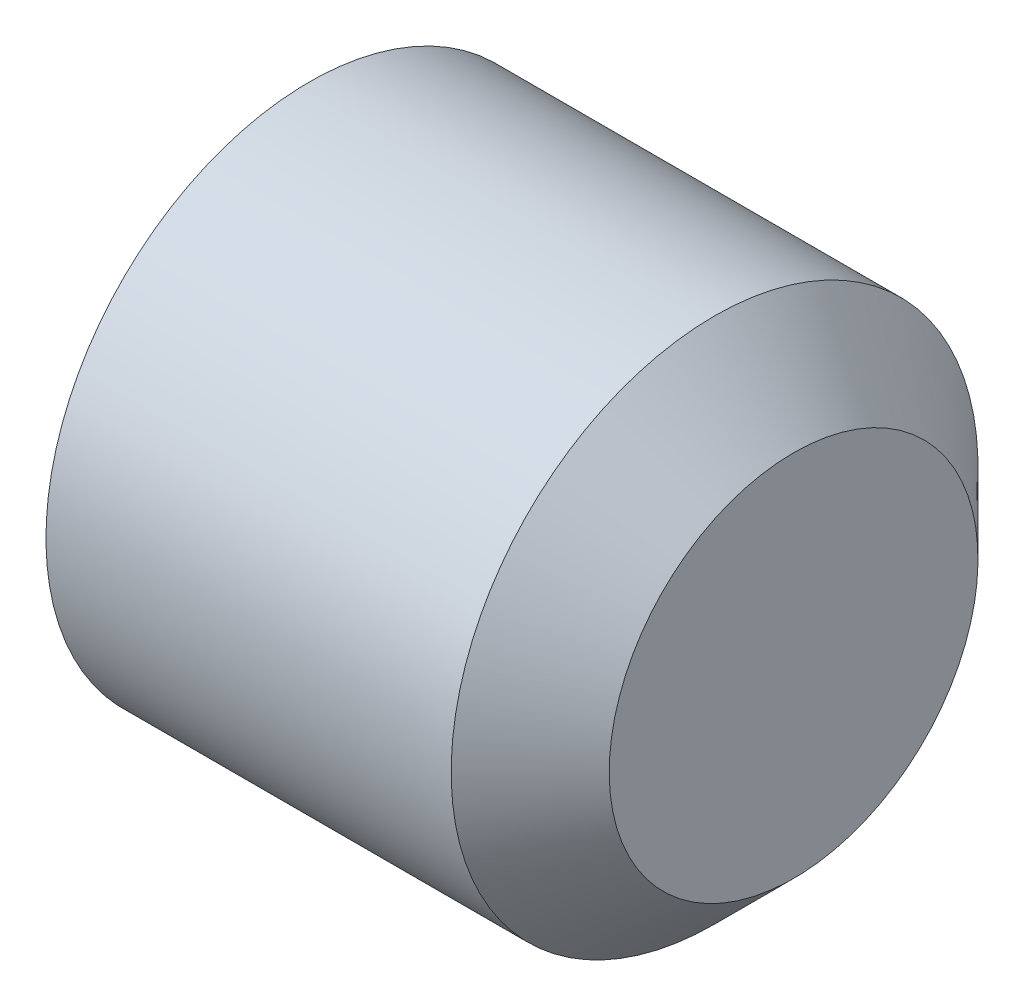
SolidWorks part; units mm, degrees
ref_plane "Спереди" through (0, 0, 0) normal (0, 0, 1) x (1, 0, 0)
ref_plane "Сверху" through (0, 0, 0) normal (0, 1, 0) x (1, 0, 0)
ref_plane "Справа" through (0, 0, 0) normal (1, 0, 0) x (0, 0, -1)
ref_plane "Плоскость1" through (0, 0, 0) normal (0, 0, -1) x (-1, 0, 0)
sketch "Эскиз1" plane through (0, 0, 0) normal (0, 0, -1) x (-1, 0, 0)
  line L0 (-5, 2.5) -> (-5, 0)
  line L1 (-5, 0) -> (0, 0)
  line L2 (0, 0) -> (0, 2.5)
  line L3 (0, 2.5) -> (-5, 2.5)
  line L4 (-5, 0) -> (0, 0) construction
  dimension "D1" = 2.5
  dimension "D2" = 5
revolve "Повернуть1" add sketch "Эскиз1" angle 360 about L4
sketch "Эскиз2" plane through (0, 0, 0) normal (-1, 0, 0) x (0, 0, 1)
  line L1 (0.7217, -1.25) -> (1.4434, 0)
  line L2 (1.4434, 0) -> (0.7217, 1.25)
  line L3 (0.7217, 1.25) -> (-0.7217, 1.25)
  line L4 (-0.7217, 1.25) -> (-1.4434, 0)
  line L5 (-1.4434, 0) -> (-0.7217, -1.25)
  line L6 (-0.7217, -1.25) -> (0.7217, -1.25)
  circle A0 centre (0, 0) radius 1.25 construction
  dimension "D1" = 1.25
extrude "Вырез-Вытянуть1" cut sketch "Эскиз2" against normal blind 1.5
chamfer "Фаска1" distance 0.75 angle 45 1 edges at (5, -2.5, 0)
chamfer "Фаска2" distance 0.7 angle 30 1 edges at (0, -2.5, 0)
fillet "Скругление1" radius 0.1 13 edges at (1.5, -0.625, -1.0825) (1.5, 0.625, -1.0825) (1.5, 1.25, 0) (1.5, 0.625, 1.0825) (1.5, -0.625, 1.0825) (1.5, -1.25, 0) (0, -0.625, 1.0825) (0, 0.625, 1.0825) (0, 1.25, 0) (0, 0.625, -1.0825) (0, -0.625, -1.0825) (0, -1.25, 0) (0, -1.8, 0)
